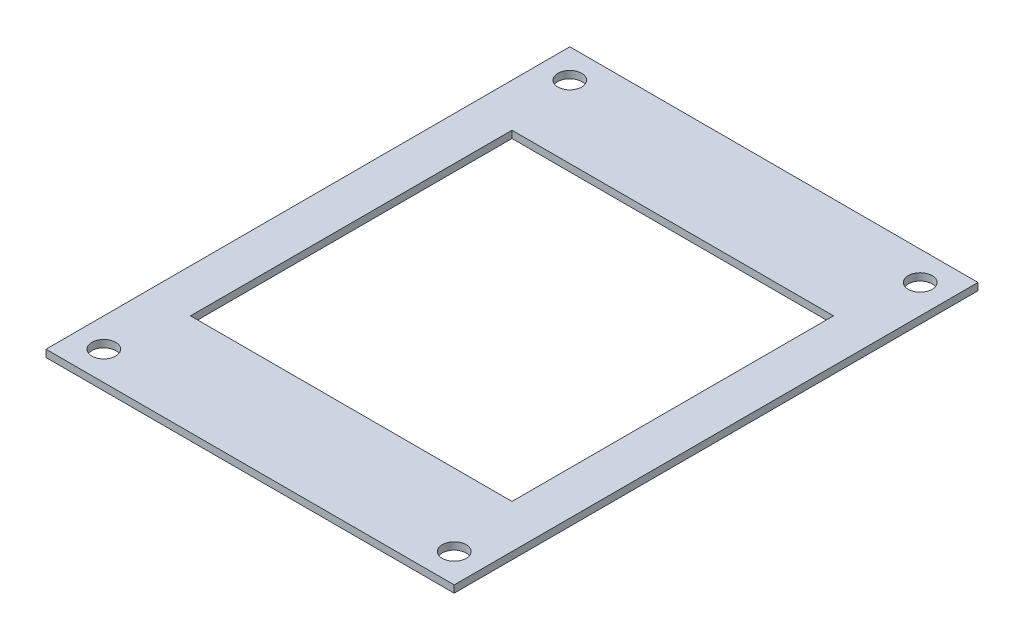
SolidWorks part; units mm, degrees
ref_plane "Front Plane" through (0, 0, 0) normal (0, 0, 1) x (1, 0, 0)
ref_plane "Top Plane" through (0, 0, 0) normal (0, 1, 0) x (1, 0, 0)
ref_plane "Right Plane" through (0, 0, 0) normal (1, 0, 0) x (0, 0, -1)
sketch "Sketch1" plane through (0, 0, 0) normal (0, 1, 0) x (1, 0, 0)
  line L0 (-28.25, -36.25) -> (28.25, -36.25)
  line L1 (-22.25, 22.25) -> (22.25, 22.25)
  line L2 (-22.25, 22.25) -> (-22.25, -22.25)
  line L3 (-22.25, -22.25) -> (22.25, -22.25)
  line L4 (22.25, 22.25) -> (22.25, -22.25)
  line L5 (-22.25, 22.25) -> (22.25, -22.25) construction
  line L6 (-22.25, -22.25) -> (22.25, 22.25) construction
  line L7 (28.25, -36.25) -> (28.25, 36.25)
  line L8 (28.25, 36.25) -> (-28.25, 36.25)
  line L9 (-28.25, 36.25) -> (-28.25, -36.25)
  circle A0 centre (-24.25, 32.25) radius 1.65
  circle A1 centre (24.25, 32.25) radius 1.65
  circle A2 centre (24.25, -32.25) radius 1.65
  circle A3 centre (-24.25, -32.25) radius 1.65
  point P0 (0, 0)
  point P18 (28.25, 0)
  point P19 (0, -36.25)
  dimension "D3" = 3.3
  dimension "D4" = 4
  dimension "D5" = 4
  dimension "D6" = 4
  dimension "D7" = 4
  dimension "D10" = 4
  dimension "D12" = 4
  dimension "D13" = 4
  dimension "D1" = 44.5
  dimension "D2" = 44.5
  dimension "D8" = 72.5
  dimension "D9" = 56.5
  dimension "D11" = 4
extrude "Boss-Extrude1" add sketch "Sketch1" along normal blind 1 contours L2 L3 L4 L1
